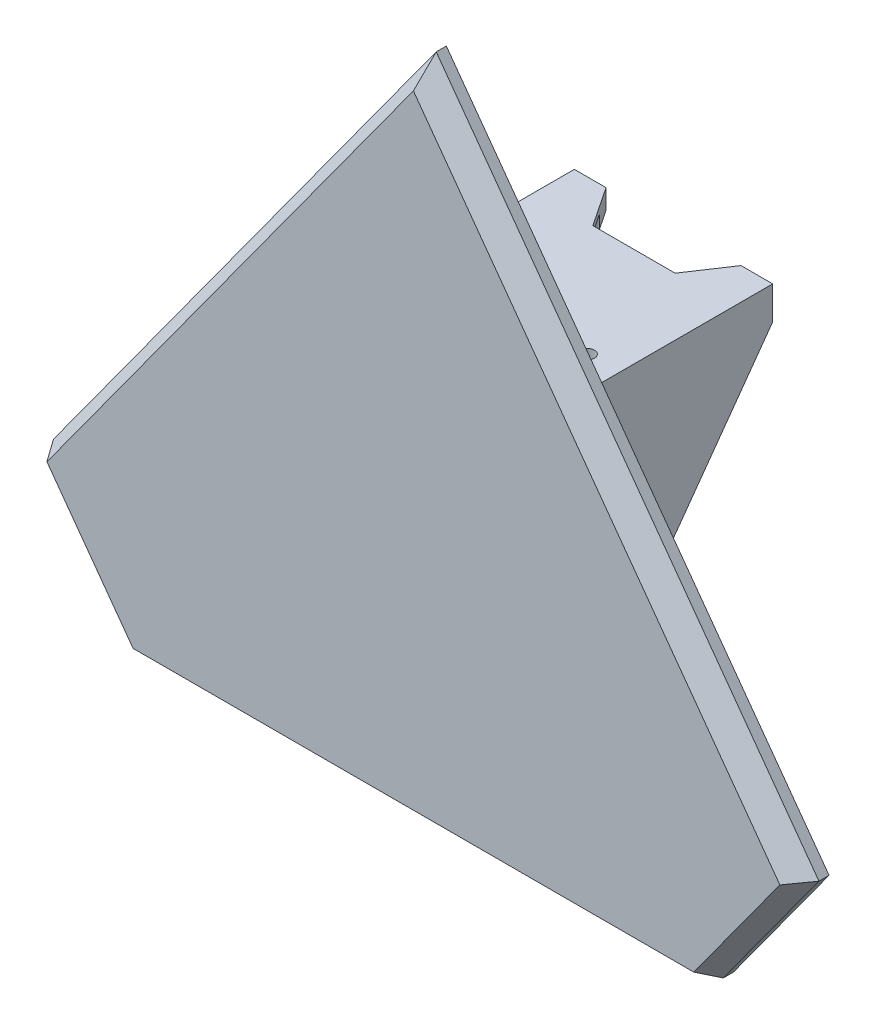
SolidWorks part; units mm, degrees
ref_plane "Front Plane" through (0, 0, 0) normal (0, 0, 1) x (1, 0, 0)
ref_plane "Top Plane" through (0, 0, 0) normal (0, 1, 0) x (1, 0, 0)
ref_plane "Right Plane" through (0, 0, 0) normal (1, 0, 0) x (0, 0, -1)
sketch "Sketch2" plane through (0, 0, 0) normal (0, 1, 0) x (1, 0, 0)
  line L0 (15.061, 0) -> (15.061, 32)
  line L1 (-12.561, 2.5) -> (12.561, 2.5)
  line L2 (-12.561, 2.5) -> (-12.561, 32)
  line L4 (12.561, 2.5) -> (12.561, 32)
  line L5 (15.061, 32) -> (12.561, 32)
  line L7 (-15.061, 32) -> (-15.061, 0)
  line L8 (-15.061, 0) -> (15.061, 0)
  line L10 (-15.061, 32) -> (-12.561, 32)
  point P4 (0, 2.5)
  point P12 (0, 0)
  dimension "D1" = 2.5
  dimension "D2" = 2.5
  dimension "D3" = 29.5
  dimension "D4" = 25.122
extrude "Boss-Extrude1" add sketch "Sketch2" along normal blind 32.5
sketch "Sketch4" plane through (0, 0, 0) normal (0, -1, 0) x (1, 0, 0)
  line L4 (-7.5, -6) -> (7.5, -6)
  line L9 (15.061, 0) -> (-15.061, 0)
  line L13 (-12.561, -2.5) -> (-12.561, -32) construction
  line L18 (-12.561, -10) -> (-7.5, -6)
  line L23 (12.561, -32) -> (12.561, -2.5) construction
  line L26 (12.561, -10) -> (7.5, -6)
  line L32 (-12.561, -10) -> (-15.061, -10)
  line L33 (-15.061, -32) -> (-15.061, 0) construction
  line L34 (-15.061, -10) -> (-15.061, 0)
  line L35 (12.561, -10) -> (15.061, -10)
  line L36 (15.061, 0) -> (15.061, -32) construction
  line L37 (15.061, -10) -> (15.061, 0)
  circle A2 centre (-10.2499, -4.95) radius 1.05
  circle A5 centre (10.2499, -4.95) radius 1.05
  point P31 (0, -6)
  dimension "D5" = 2.1
  dimension "D10" = 15
  dimension "D11" = 10
  dimension "D2" = 6
  dimension "D7" = 4.95
extrude "Boss-Extrude2" add sketch "Sketch4" along normal blind 2.5
sketch "Sketch5" plane through (0, 32.5, 0) normal (0, 1, 0) x (1, 0, 0)
  line L0 (-15.061, 32) -> (-10.2499, 32)
  line L9 (-10.2499, 32) -> (-6.25, 26)
  line L13 (-15.061, 0) -> (15.061, 0) construction
  line L14 (15.061, 0) -> (-15.061, 0)
  line L15 (-15.061, 0) -> (-15.061, 32)
  line L20 (15.061, 0) -> (15.061, 32)
  line L21 (-6.25, 26) -> (6.25, 26)
  line L22 (6.25, 26) -> (10.2499, 32)
  line L23 (10.2499, 32) -> (15.061, 32)
  circle A0 centre (-10.2499, 4.95) radius 1.05 construction
  circle A1 centre (-10.2499, 8.7) radius 1.05
  circle A2 centre (10.2499, 8.7) radius 1.05
  point P6 (0, 26)
  dimension "D4" = 0
  dimension "D1" = 8.7
  dimension "D2" = 12.5
  dimension "D3" = 20.4998
  dimension "D5" = 6
extrude "Boss-Extrude3" add sketch "Sketch5" along normal blind 3
sketch "Sketch6" plane through (-15.061, 0, 0) normal (-1, 0, 0) x (0, 0, 1)
  line L0 (-10, 0) -> (-32, 30.5)
  line L1 (-32, 30.5) -> (-32, 0)
  line L2 (-32, 0) -> (-10, 0)
  line L3 (-32, 35.5) -> (-32, 0) construction
  dimension "D1" = 5
extrude "Cut-Extrude1" cut sketch "Sketch6" against normal through all
ref_plane "Plane1" through (0, 16.5, 0) normal (0, -1, 0) x (-1, 0, 0)
sketch "Sketch13" plane through (0, 0, 0) normal (0, 0, 1) x (1, 0, 0)
  line L1 (-15.061, 35.5) -> (15.061, 35.5)
  line L2 (-15.061, 35.5) -> (-15.061, -2.5)
  line L3 (-15.061, -2.5) -> (15.061, -2.5)
  line L4 (15.061, 35.5) -> (15.061, -2.5)
extrude "Boss-Extrude7" add sketch "Sketch13" along normal blind 2.5
sketch "Sketch8" plane through (0, 0, 2.5) normal (0, 0, 1) x (1, 0, 0)
  line L0 (0, 76.5) -> (43.5926, 16.5)
  line L1 (-16.5671, 16.5) -> (16.5671, 16.5) construction
  line L2 (43.5926, 16.5) -> (-43.5926, 16.5)
  line L3 (-43.5926, 16.5) -> (0, 76.5)
  dimension "D1" = 72
  dimension "D2" = 60
extrude "Boss-Extrude4" add sketch "Sketch8" along normal blind 5
sketch "Sketch9" plane through (0, 0, 2.5) normal (0, 0, 1) x (1, 0, 0)
  line L0 (-43.5926, 16.5) -> (-72.6543, -23.5)
  line L1 (-72.6543, -23.5) -> (72.6543, -23.5)
  line L2 (72.6543, -23.5) -> (43.5926, 16.5)
  line L3 (-43.5926, 16.5) -> (43.5926, 16.5)
  line L4 (0, 76.5) -> (-43.5926, 16.5) construction
  line L5 (43.5926, 16.5) -> (0, 76.5) construction
  dimension "D1" = 40
extrude "Boss-Extrude6" add sketch "Sketch9" along normal up to surface (5 mm away) up to face at (0, 36.5, 7.5)
sketch "Sketch10" plane through (0, 0, 2.5) normal (0, 0, -1) x (-1, 0, 0)
  line L0 (-43.5926, -23.5) -> (-58.1234, -3.5)
  line L1 (72.6543, -23.5) -> (-72.6543, -23.5) construction
  line L2 (-72.6543, -23.5) -> (0, 76.5) construction
  line L3 (-58.1234, -3.5) -> (-72.6543, -23.5)
  line L4 (-72.6543, -23.5) -> (-43.5926, -23.5)
  line L5 (72.6543, -23.5) -> (58.1234, -3.5)
  line L13 (0, 76.5) -> (72.6543, -23.5) construction
  line L14 (58.1234, -3.5) -> (43.5926, -23.5)
  line L15 (72.6543, -23.5) -> (-72.6543, -23.5) construction
  line L16 (43.5926, -23.5) -> (72.6543, -23.5)
  point P13 (58.1234, -23.5)
  dimension "D1" = 20
extrude "Cut-Extrude2" cut sketch "Sketch10" against normal through all
sketch "Sketch12" plane through (0, 0, -26) normal (0, 0, -1) x (-1, 0, 0)
  line L1 (-8.2499, 34.5) -> (8.2499, 34.5)
  line L2 (-8.2499, 34.5) -> (-8.2499, 32.5)
  line L3 (-8.2499, 32.5) -> (8.2499, 32.5)
  line L4 (8.2499, 34.5) -> (8.2499, 32.5)
  line L5 (6.25, 32.5) -> (10.2499, 32.5) construction
  line L6 (-10.2499, 35.5) -> (-6.25, 35.5) construction
  point P8 (-8.2499, 35.5)
  dimension "D1" = 2
extrude "Cut-Extrude4" cut sketch "Sketch12" against normal up to surface (23.5 mm away) and the other way blind 10 up to face at (0, 16.25, -2.5)
chamfer "Chamfer1" distance 2 angle 60 5 edges at (-50.858, -13.5, 7.5) (-29.0617, 36.5, 7.5) (29.0617, 36.5, 7.5) (50.858, -13.5, 7.5) (0, -23.5, 7.5)
